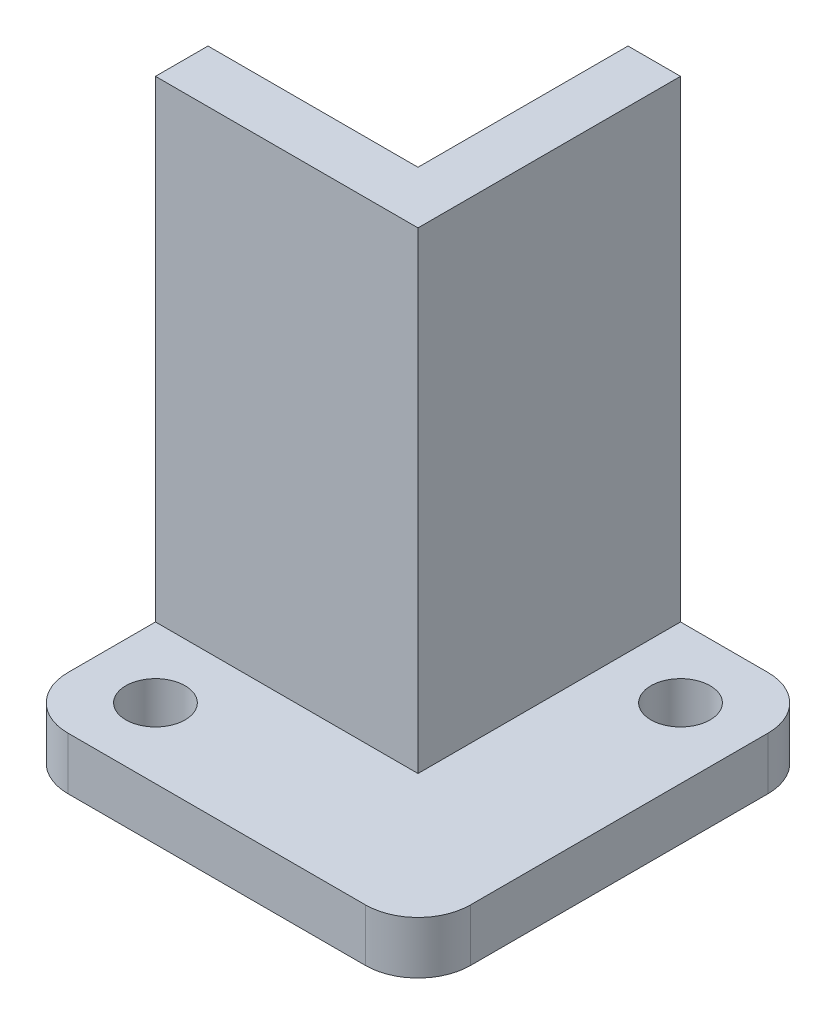
SolidWorks part; units mm, degrees
ref_plane "Front Plane" through (0, 0, 0) normal (0, 0, 1) x (1, 0, 0)
ref_plane "Top Plane" through (0, 0, 0) normal (0, 1, 0) x (1, 0, 0)
ref_plane "Right Plane" through (0, 0, 0) normal (1, 0, 0) x (0, 0, -1)
sketch "Sketch1" plane through (0, 0, 0) normal (0, 1, 0) x (1, 0, 0)
  line L0 (29.21, 0) -> (29.21, 29.21)
  line L1 (0, 0) -> (29.21, 0)
  line L2 (0, 0) -> (0, 13.97)
  line L3 (0, 13.97) -> (15.24, 13.97)
  line L7 (29.21, 29.21) -> (15.24, 29.21)
  line L8 (15.24, 13.97) -> (15.24, 29.21)
  dimension "D1" = 13.97
  dimension "D2" = 29.21
extrude "Boss-Extrude1" add sketch "Sketch1" along normal blind 3.81
sketch "Sketch2" plane through (0, 3.81, 0) normal (0, 1, 0) x (1, 0, 0)
  line L0 (29.21, 29.21) -> (15.24, 29.21) construction
  line L1 (0, 13.97) -> (15.24, 13.97)
  line L2 (0, 13.97) -> (0, 10.16)
  line L3 (0, 10.16) -> (19.05, 10.16)
  line L7 (19.05, 29.21) -> (15.24, 29.21)
  line L8 (15.24, 13.97) -> (15.24, 29.21)
  line L9 (15.24, 29.21) -> (15.24, 13.97) construction
  line L10 (19.05, 10.16) -> (19.05, 29.21)
  dimension "D1" = 3.81
extrude "Boss-Extrude2" add sketch "Sketch2" along normal blind 34.29
sketch "Sketch3" plane through (0, 3.81, 0) normal (0, 1, 0) x (1, 0, 0)
  line L0 (29.21, 0) -> (29.21, 29.21) construction
  line L1 (29.21, 29.21) -> (19.05, 29.21) construction
  line L2 (0, 0) -> (29.21, 0) construction
  line L3 (0, 10.16) -> (0, 0) construction
  circle A0 centre (5.08, 5.08) radius 2.15
  circle A1 centre (24.13, 24.13) radius 2.15
  dimension "D5" = 4.3
  dimension "D1" = 5.08
  dimension "D2" = 5.08
  dimension "D3" = 5.08
  dimension "D4" = 5.08
extrude "Cut-Extrude1" cut sketch "Sketch3" against normal through all
fillet "Fillet1" radius 3.81 3 edges at (29.21, 1.905, -29.21) (29.21, 1.905, 0) (0, 1.905, 0)
